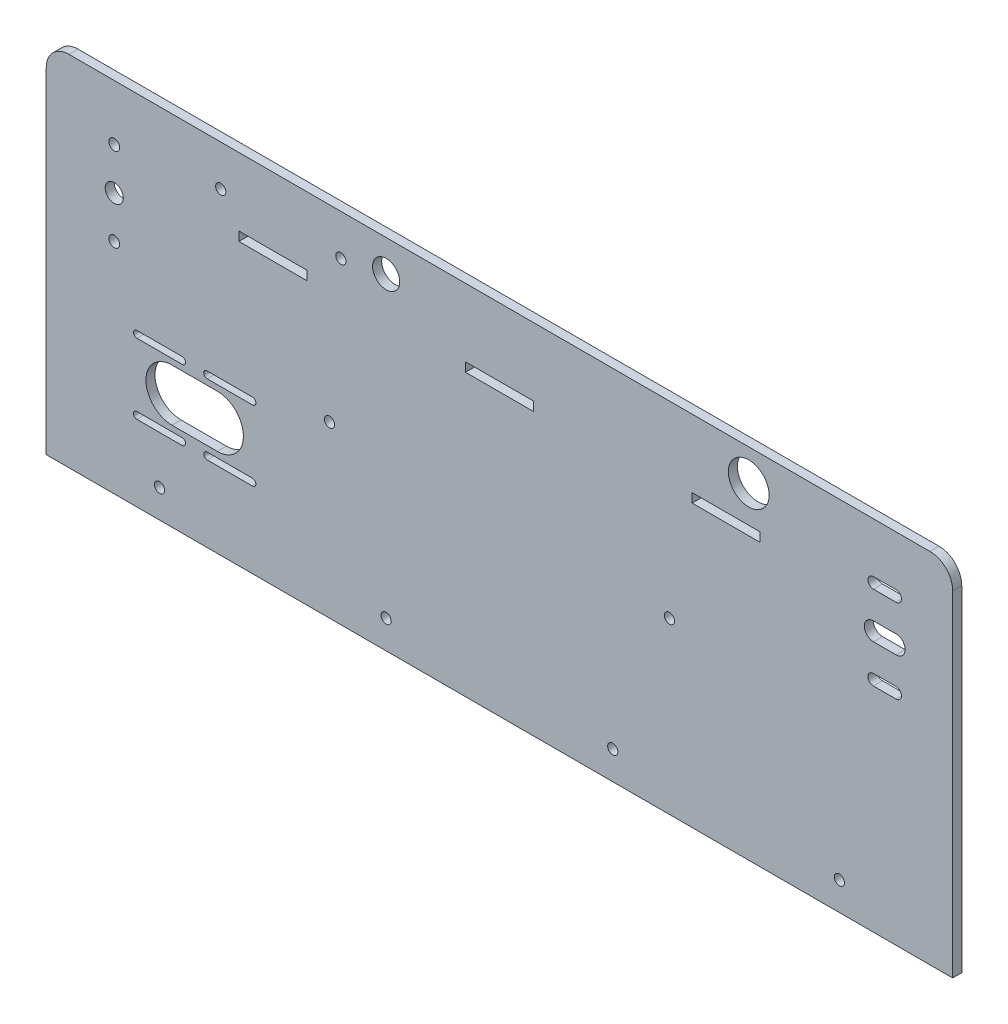
SolidWorks part; units mm, degrees
material "Acrílico (médio-alto impacto)"
ref_plane "Plano frontal" through (0, 0, 0) normal (0, 0, 1) x (1, 0, 0)
ref_plane "Plano superior" through (0, 0, 0) normal (0, 1, 0) x (1, 0, 0)
ref_plane "Plano direito" through (0, 0, 0) normal (1, 0, 0) x (0, 0, -1)
sketch "Esboço1" plane through (0, 0, 0) normal (0, 0, 1) x (1, 0, 0)
  line L0 (0, 0) -> (400, 0)
  line L2 (10, 150) -> (50, 150)
  line L3 (60, 130) -> (60, 140)
  line L4 (60, 130) -> (120, 130)
  line L5 (120, 130) -> (120, 140)
  line L6 (130, 150) -> (390, 150)
  line L7 (400, 140) -> (400, 0)
  line L8 (0, 140) -> (0, 0)
  line L9 (30, 133.5) -> (30, 96.5) construction
  line L10 (85, 126) -> (115, 126) construction
  line L11 (85, 124) -> (115, 124)
  line L12 (85, 124) -> (85, 128)
  line L13 (85, 128) -> (115, 128)
  line L14 (115, 124) -> (115, 128)
  line L15 (185, 124) -> (215, 124)
  line L16 (185, 128) -> (215, 128)
  line L17 (215, 124) -> (215, 128)
  line L18 (185, 126) -> (215, 126) construction
  line L19 (185, 124) -> (185, 128)
  line L20 (285, 124) -> (315, 124)
  line L21 (285, 128) -> (315, 128)
  line L22 (315, 124) -> (315, 128)
  line L23 (285, 126) -> (315, 126) construction
  line L24 (285, 124) -> (285, 128)
  line L25 (150, 144) -> (310, 144) construction
  line L29 (301, 144) -> (319, 144) construction
  line L37 (301, 144) -> (301, 150) construction
  line L42 (301, 150) -> (319, 150)
  line L50 (319, 144) -> (319, 150) construction
  line L61 (50, 150) -> (130, 150)
  line L62 (365, 133.5) -> (375, 133.5) construction
  line L63 (365, 135.9) -> (375, 135.9)
  line L64 (365, 131.1) -> (375, 131.1)
  line L65 (365, 96.5) -> (375, 96.5) construction
  line L66 (365, 98.9) -> (375, 98.9)
  line L67 (365, 94.1) -> (375, 94.1)
  line L68 (370, 133.5) -> (370, 96.5) construction
  circle A1 centre (30, 96.5) radius 2.4
  circle A2 centre (30, 133.5) radius 2.4
  arc A3 (60, 140) -> (50, 150) centre (50, 140) ccw
  arc A4 (390, 150) -> (400, 140) centre (390, 140) cw
  arc A5 (0, 140) -> (10, 150) centre (10, 140) cw
  arc A6 (120, 140) -> (130, 150) centre (130, 140) cw
  arc A9 (365, 135.9) -> (365, 131.1) centre (365, 133.5) ccw
  arc A10 (375, 131.1) -> (375, 135.9) centre (375, 133.5) ccw
  arc A11 (365, 98.9) -> (365, 94.1) centre (365, 96.5) ccw
  arc A12 (375, 94.1) -> (375, 98.9) centre (375, 96.5) ccw
  circle A13 centre (150, 144) radius 6 construction
  circle A14 centre (310, 144) radius 9 construction
  point P3 (30, 115)
  point P16 (60, 150)
  point P21 (0, 150)
  point P30 (200, 126)
  point P32 (370, 115)
  point P75 (370, 133.5)
  point P100 (370, 96.5)
  dimension "D6" = 37
  dimension "D7" = 4.8
  dimension "D8" = 4.8
  dimension "D11" = 10
  dimension "D12" = 10
  dimension "D19" = 18
  dimension "D20" = 150
  dimension "D35" = 2.4
  dimension "D37" = 2.4
  dimension "D18" = 12
  dimension "D1" = 400
  dimension "D2" = 150
  dimension "D3" = 60
  dimension "D4" = 20
  dimension "D5" = 60
  dimension "D9" = 30
  dimension "D10" = 35
  dimension "D13" = 4
  dimension "D14" = 30
  dimension "D15" = 2
  dimension "D17" = 70
  dimension "D21" = 60
  dimension "D23" = 144
  dimension "D33" = 200
  dimension "D34" = 10
  dimension "D36" = 10
  dimension "D38" = 37
  dimension "D39" = 30
  dimension "D40" = 35
  dimension "D22" = 310
  dimension "D16" = 3
extrude "Ressalto-extrusão1" add sketch "Esboço1" along normal blind 4
sketch "Esboço3" plane through (0, 0, 4) normal (0, 0, 1) x (1, 0, 0)
  line L0 (365, 115) -> (375, 115) construction
  line L1 (365, 119) -> (375, 119)
  line L2 (365, 111) -> (375, 111)
  line L3 (40, 66) -> (60, 66) construction
  line L17 (0, 140) -> (0, 0) construction
  line L18 (0, 0) -> (400, 0) construction
  line L22 (30, 133.5) -> (30, 96.5) construction
  line L24 (370, 131.1) -> (370, 98.9) construction
  line L25 (365, 131.1) -> (375, 131.1) construction
  line L26 (365, 98.9) -> (375, 98.9) construction
  line L27 (40, 67.5) -> (60, 67.5)
  line L28 (40, 64.5) -> (60, 64.5)
  line L29 (71, 35) -> (91, 35) construction
  line L30 (71, 36.5) -> (91, 36.5)
  line L31 (71, 33.5) -> (91, 33.5)
  line L32 (71, 66) -> (91, 66) construction
  line L33 (71, 67.5) -> (91, 67.5)
  line L34 (71, 64.5) -> (91, 64.5)
  line L35 (40, 35) -> (60, 35) construction
  line L36 (40, 36.5) -> (60, 36.5)
  line L37 (40, 33.5) -> (60, 33.5)
  line L38 (60, 66) -> (71, 66) construction
  line L40 (60, 35) -> (71, 35) construction
  line L41 (65.5, 66) -> (65.5, 35) construction
  line L42 (55.5, 50.5) -> (75.5, 50.5) construction
  line L43 (55.5, 62) -> (75.5, 62)
  line L44 (55.5, 39) -> (75.5, 39)
  arc A0 (365, 119) -> (365, 111) centre (365, 115) ccw
  arc A1 (375, 111) -> (375, 119) centre (375, 115) ccw
  circle A2 centre (30, 115) radius 4
  arc A9 (40, 67.5) -> (40, 64.5) centre (40, 66) ccw
  arc A10 (60, 64.5) -> (60, 67.5) centre (60, 66) ccw
  arc A11 (71, 36.5) -> (71, 33.5) centre (71, 35) ccw
  arc A12 (91, 33.5) -> (91, 36.5) centre (91, 35) ccw
  arc A13 (71, 67.5) -> (71, 64.5) centre (71, 66) ccw
  arc A14 (91, 64.5) -> (91, 67.5) centre (91, 66) ccw
  arc A15 (40, 36.5) -> (40, 33.5) centre (40, 35) ccw
  arc A16 (60, 33.5) -> (60, 36.5) centre (60, 35) ccw
  arc A17 (55.5, 62) -> (55.5, 39) centre (55.5, 50.5) ccw
  arc A18 (75.5, 39) -> (75.5, 62) centre (75.5, 50.5) ccw
  point P2 (370, 115)
  point P44 (370, 115)
  point P49 (30, 115)
  point P56 (50, 66)
  point P63 (81, 35)
  point P70 (81, 66)
  point P77 (50, 35)
  point P86 (65.5, 50.5)
  point P96 (65.5, 50.5)
  dimension "D2" = 4
  dimension "D5" = 8
  dimension "D15" = 40
  dimension "D16" = 35
  dimension "D3" = 1.5
  dimension "D6" = 1.5
  dimension "D24" = 1.5
  dimension "D26" = 1.5
  dimension "D31" = 11.5
  dimension "D1" = 10
  dimension "D4" = 20
  dimension "D7" = 20
  dimension "D25" = 20
  dimension "D27" = 20
  dimension "D28" = 31
  dimension "D29" = 31
  dimension "D30" = 31
  dimension "D32" = 20
extrude "Corte-extrusão1" cut sketch "Esboço3" against normal blind 6
hole_wizard "Furo com folga de M41" positions "3DSketch1" profile "Esboço4" hole size "M4" standard "ISO" end condition through all
sketch3d "3DSketch1"
  line L0 (125, 75, 4) -> (275, 75, 4) construction
  line L2 (400, 140, 4) -> (400, 0, 4) construction
  line L3 (0, 140, 4) -> (0, 0, 4) construction
  line L4 (0, 0, 4) -> (400, 0, 4) construction
  line L5 (50, 12.5, 4) -> (350, 12.5, 4) construction
  line L6 (77, 140, 4) -> (130, 140, 4) construction
  line L8 (150, 141, 4) -> (150, 150, 4) construction
  line L10 (10, 150, 4) -> (390, 150, 4) construction
  point P0 (50, 12.5, 4)
  point P2 (150, 12.5, 4)
  point P4 (250, 12.5, 4)
  point P6 (350, 12.5, 4)
  point P8 (275, 75, 4)
  point P10 (125, 75, 4)
  point P60 (77, 140, 4)
  point P62 (130, 140, 4)
  dimension "D1" = 125
  dimension "D2" = 125
  dimension "D3" = 75
  dimension "D4" = 100
  dimension "D5" = 100
  dimension "D6" = 50
  dimension "D7" = 50
  dimension "D8" = 12.5
  dimension "D9" = 53
  dimension "D10" = 10
  dimension "D11" = 20
sketch "Esboço4" plane through (50, 12.5, 4) normal (1, 0, 0) x (0, -1, 0)
  line L0 (0, 0) -> (0, 4)
  line L1 (0, 4) -> (2.25, 4)
  line L2 (2.25, 4) -> (2.25, 0)
  line L5 (2.25, 0) -> (0, 0)
  line L11 (0, -6.35) -> (0, 107.95) construction
  dimension "Thru Hole Dia." = 4.5
  dimension "Thru Hole Depth" = 4
sketch "Esboço5" plane through (0, 0, 4) normal (0, 0, 1) x (1, 0, 0)
  line L0 (0, 140) -> (0, 148)
  line L1 (10, 158) -> (390, 158)
  line L2 (400, 148) -> (400, 140)
  line L3 (10, 150) -> (390, 150) construction
  line L4 (10, 150) -> (390, 150)
  arc A0 (400, 140) -> (390, 150) centre (390, 140) ccw construction
  arc A1 (10, 150) -> (0, 140) centre (10, 140) ccw construction
  arc A2 (400, 140) -> (390, 150) centre (390, 140) ccw
  arc A3 (10, 150) -> (0, 140) centre (10, 140) ccw
  arc A4 (0, 148) -> (10, 158) centre (10, 148) cw
  arc A5 (390, 158) -> (400, 148) centre (390, 148) cw
  dimension "D2" = 10
  dimension "D1" = 8
extrude "Ressalto-extrusão2" add sketch "Esboço5" against normal up to surface (4 mm away) up to face at (52.25, 12.5, 0)
sketch "Esboço8" plane through (0, 0, 0) normal (0, 0, 1) x (1, 0, 0)
  circle A0 centre (150, 144) radius 6 construction
  circle A1 centre (150, 144) radius 6
  circle A2 centre (310, 144) radius 9 construction
  circle A3 centre (310, 144) radius 9
extrude "Corte-extrusão4" cut sketch "Esboço8" along normal through all
